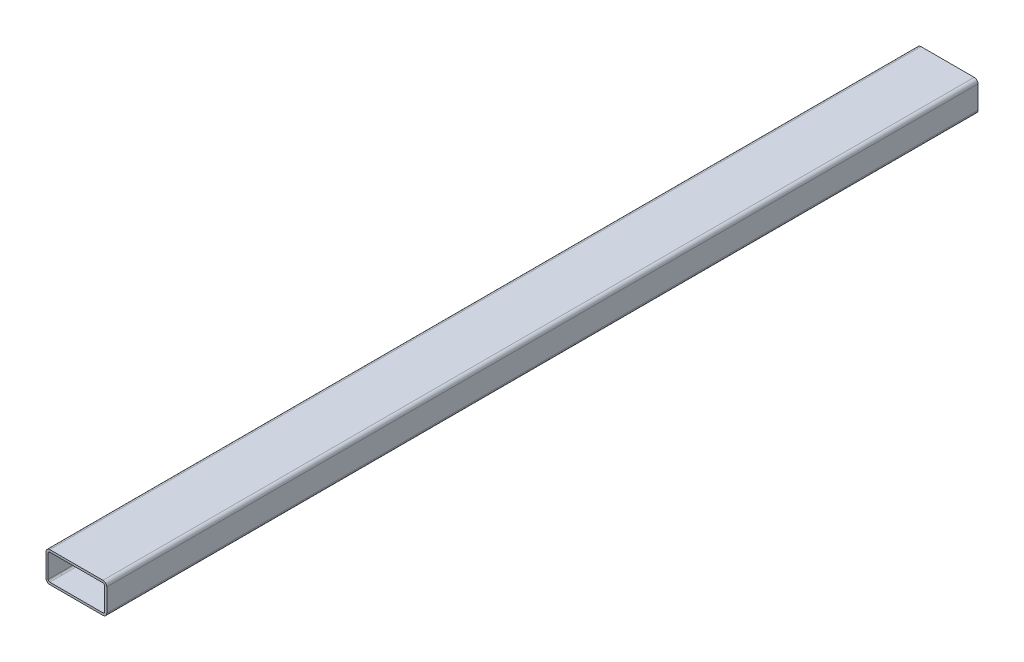
SolidWorks part; units mm, degrees
ref_plane "Front Plane" through (0, 0, 0) normal (0, 0, 1) x (1, 0, 0)
ref_plane "Top Plane" through (0, 0, 0) normal (0, 1, 0) x (1, 0, 0)
ref_plane "Right Plane" through (0, 0, 0) normal (1, 0, 0) x (0, 0, -1)
sketch "Sketch1" plane through (0, 0, 0) normal (0, 0, 1) x (1, 0, 0)
  line L0 (-37.1, -15) -> (-37.1, 15)
  line L1 (-35, -20) -> (35, -20)
  line L2 (-40, -15) -> (-40, 15)
  line L3 (-35, 20) -> (35, 20)
  line L4 (40, -15) -> (40, 15)
  line L5 (-40, -20) -> (40, 20) construction
  line L6 (-40, 20) -> (40, -20) construction
  line L7 (-35, 17.1) -> (35, 17.1)
  line L8 (37.1, -15) -> (37.1, 15)
  line L9 (-35, -17.1) -> (35, -17.1)
  arc A0 (35, -20) -> (40, -15) centre (35, -15) ccw
  arc A1 (-35, -20) -> (-40, -15) centre (-35, -15) cw
  arc A2 (35, 20) -> (40, 15) centre (35, 15) cw
  arc A3 (-40, 15) -> (-35, 20) centre (-35, 15) cw
  arc A4 (-37.1, 15) -> (-35, 17.1) centre (-35, 15) cw
  arc A5 (35, 17.1) -> (37.1, 15) centre (35, 15) cw
  arc A6 (35, -17.1) -> (37.1, -15) centre (35, -15) ccw
  arc A7 (-35, -17.1) -> (-37.1, -15) centre (-35, -15) cw
  point P0 (0, 0)
  dimension "D3" = 5
  dimension "D1" = 40
  dimension "D2" = 80
  dimension "D4" = 2.9
extrude "Boss-Extrude1" add sketch "Sketch1" along normal blind 1146.7
equation "\"tube height\"= \"D1@Sketch1\""
equation "\"tube width\"= \"D2@Sketch1\""
equation "\"tube thickness\"= \"D4@Sketch1\""
equation "\"tube radius\"= \"D4@Sketch1\""
